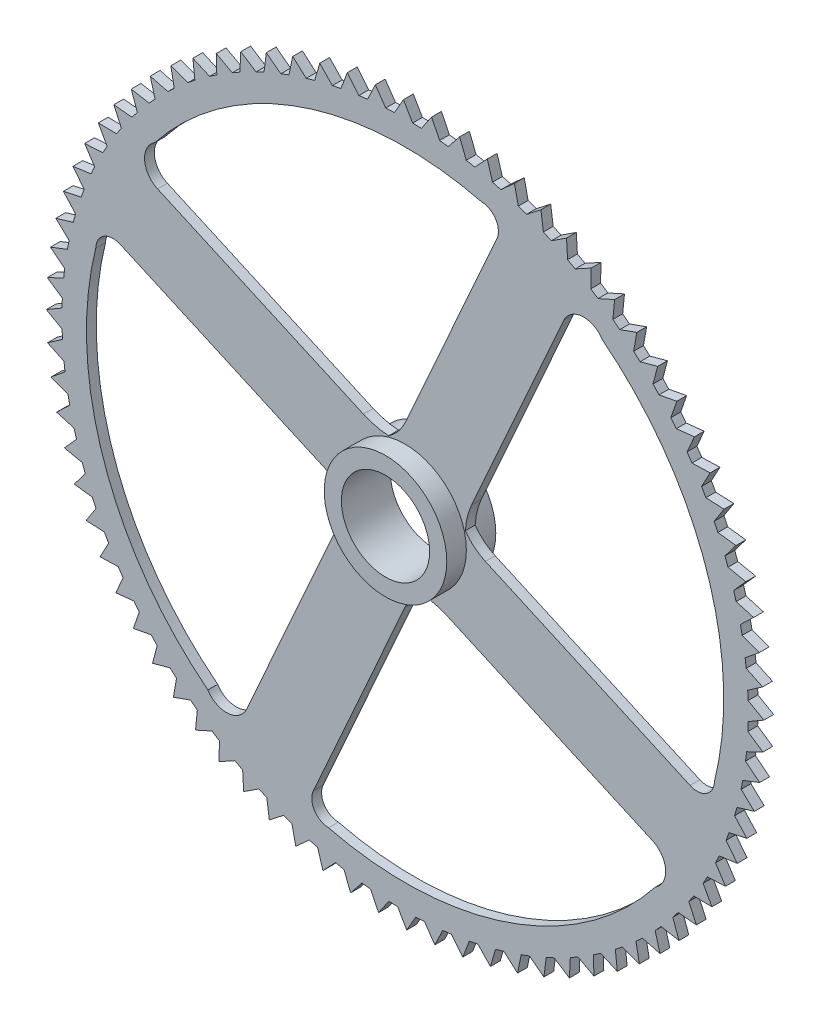
SolidWorks part; units mm, degrees
ref_plane "Front Plane" through (0, 0, 0) normal (0, 0, 1) x (1, 0, 0)
ref_plane "Top Plane" through (0, 0, 0) normal (0, 1, 0) x (1, 0, 0)
ref_plane "Right Plane" through (0, 0, 0) normal (1, 0, 0) x (0, 0, -1)
sketch "Sketch1" plane through (0, 0, 0) normal (0, 0, 1) x (1, 0, 0)
  line L0 (2.9308, 70) -> (0, 70)
  line L1 (0, 70) -> (1.3564, 72.5614)
  line L2 (1.3564, 72.5614) -> (2.9308, 70)
  line L3 (0.0419, 16.3783) -> (18.7329, 58.1314)
  line L4 (13.5409, 8.5077) -> (32.3384, 50.4986)
  line L5 (8.5077, -13.5409) -> (50.4986, -32.3384)
  line L6 (16.3783, -0.0419) -> (58.1314, -18.7329)
  line L7 (-13.5409, -8.5077) -> (-32.3384, -50.4986)
  line L8 (-0.0419, -16.3783) -> (-18.7329, -58.1314)
  line L9 (-8.5077, 13.5409) -> (-50.4986, 32.3384)
  line L10 (-16.3783, 0.0419) -> (-58.1314, 18.7329)
  circle A0 centre (0, 0) radius 12.5
  circle A1 centre (0, 0) radius 70
  circle A2 centre (0, 0) radius 65
  arc A3 (18.7329, 58.1314) -> (15.627, 63.0936) centre (15.5165, 59.5713) ccw
  arc A4 (0.0419, 16.3783) -> (-3.3467, 12.2927) centre (-8.9906, 20.4217) cw
  arc A5 (32.3384, 50.4986) -> (40.2382, 51.0479) centre (36.4349, 48.6648) cw
  arc A6 (13.5409, 8.5077) -> (12.2927, 3.3467) centre (26.8129, 2.5664) ccw
  arc A7 (16.3783, -0.0419) -> (12.2927, 3.3467) centre (20.4217, 8.9906) cw
  arc A8 (8.5077, -13.5409) -> (3.3467, -12.2927) centre (2.5664, -26.8129) ccw
  arc A9 (50.4986, -32.3384) -> (51.0479, -40.2382) centre (48.6648, -36.4349) cw
  arc A10 (58.1314, -18.7329) -> (63.0936, -15.627) centre (59.5713, -15.5165) ccw
  arc A11 (-0.0419, -16.3783) -> (3.3467, -12.2927) centre (8.9906, -20.4217) cw
  arc A12 (-13.5409, -8.5077) -> (-12.2927, -3.3467) centre (-26.8129, -2.5664) ccw
  arc A13 (-32.3384, -50.4986) -> (-40.2382, -51.0479) centre (-36.4349, -48.6648) cw
  arc A14 (-18.7329, -58.1314) -> (-15.627, -63.0936) centre (-15.5165, -59.5713) ccw
  arc A15 (-16.3783, 0.0419) -> (-12.2927, -3.3467) centre (-20.4217, -8.9906) cw
  arc A16 (-8.5077, 13.5409) -> (-3.3467, 12.2927) centre (-2.5664, 26.8129) ccw
  arc A17 (-50.4986, 32.3384) -> (-51.0479, 40.2382) centre (-48.6648, 36.4349) cw
  arc A18 (-58.1314, 18.7329) -> (-63.0936, 15.627) centre (-59.5713, 15.5165) ccw
  point P59 (0, 0)
  dimension "D1" = 25
  dimension "D2" = 140
  dimension "D3" = 130
  dimension "D4" = 4
extrude "Boss-Extrude4" add sketch "Sketch1" along normal mid plane 2 contours A1 A18 A2 A17 A3 A5 A10 A9 A14 A13 | A18 L10 A15 A12 L7 A13 A2 A14 L8 A11 A8 L5 A9 A10 L6 A7 A6 L4 A5 A3 L3 A4 A16 L9 A17 A0
sketch "Sketch2" plane through (0, 0, 0) normal (0, 0, 1) x (1, 0, 0)
  circle A0 centre (0, 0) radius 12.5
  dimension "D1" = 25
extrude "Boss-Extrude6" add sketch "Sketch2" along normal mid plane 10
sketch "Sketch3" plane through (0, 0, 5) normal (0, 0, 1) x (1, 0, 0)
  circle A0 centre (0, 0) radius 9
  dimension "D1" = 18
extrude "Cut-Extrude1" cut sketch "Sketch3" against normal through all
sketch "Sketch4" plane through (0, 0, 1) normal (0, 0, 1) x (1, 0, 0)
  line L0 (-69.5799, -7.6579) -> (-72.9409, -6.0734)
  line L1 (-72.9409, -6.0734) -> (-69.8882, -3.9549)
  line L2 (-69.8882, -3.9549) -> (-69.5799, -7.6579)
  circle A1 centre (0, 0) radius 70 construction
extrude "Boss-Extrude7" add sketch "Sketch4" against normal blind 2
pattern_circular "CirPattern1" count 80 over 360 about axis through (0, 0, 0) along (0, 0, 1) of "Boss-Extrude7"
